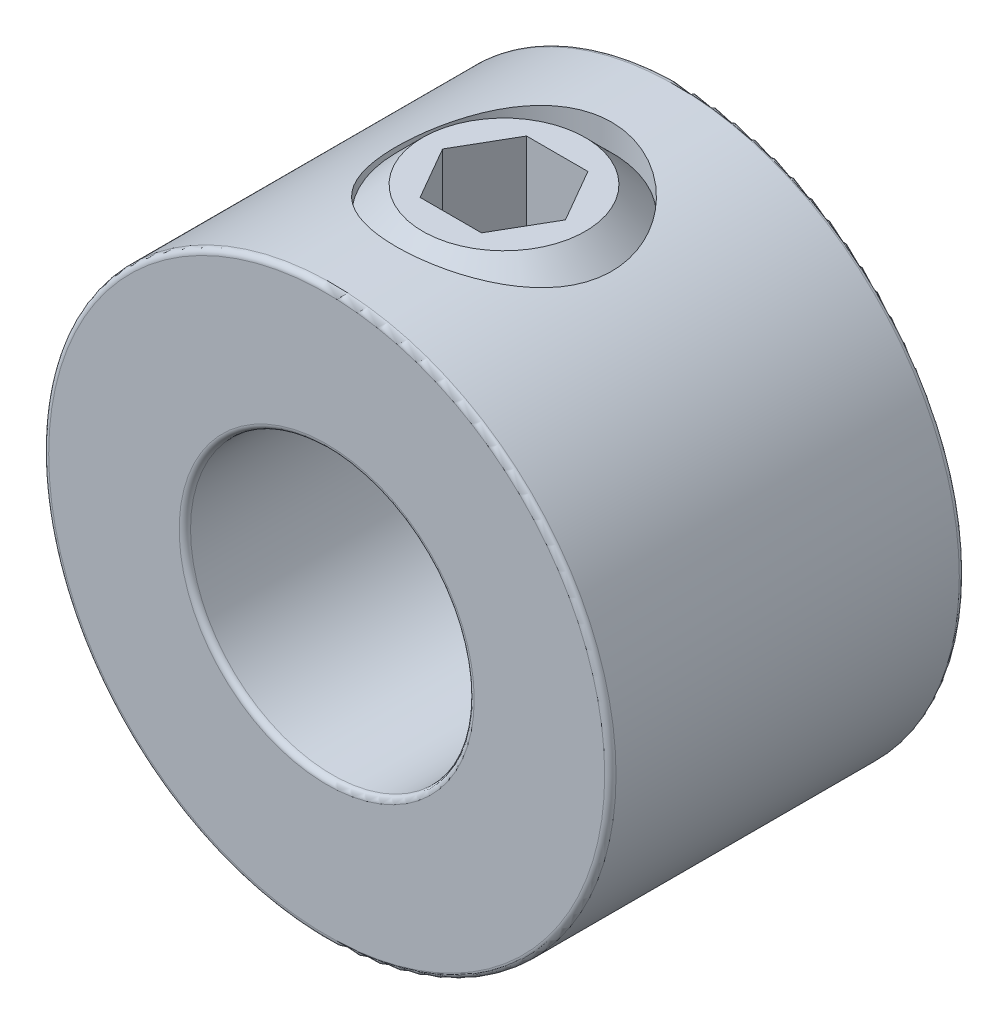
SolidWorks part; units mm, degrees
material "Alliage 1060"
ref_plane "Front Plane" through (0, 0, 0) normal (0, 0, 1) x (1, 0, 0)
ref_plane "Top Plane" through (0, 0, 0) normal (0, 1, 0) x (1, 0, 0)
ref_plane "Right Plane" through (0, 0, 0) normal (1, 0, 0) x (0, 0, -1)
sketch "Sketch1" plane through (0, 0, 0) normal (0, 0, 1) x (1, 0, 0)
  circle A0 centre (0, 0) radius 6.35
  circle A1 centre (0, 0) radius 3.175
  point P4 (6.35, 0)
  dimension "Bore Dia" = 6.35
  dimension "OD" = 12.7
extrude "Extrude1" add sketch "Sketch1" along normal mid plane 7.9375
sketch "Sketch2" plane through (41.275, 0, 0) normal (0, -1, 0) x (0, 0, -1)
  line L0 (3.9688, -41.275) -> (-3.9688, -41.275) construction
  line L1 (-3.9688, -34.925) -> (-3.9688, -47.625) construction
  line L2 (3.9688, -47.625) -> (3.9688, -34.925) construction
  circle A0 centre (0, -41.275) radius 2.413
  point P7 (0, -43.688)
  dimension "Set Screw Dia" = 4.826
extrude "Cut-Extrude1" cut sketch "Sketch2" against normal through all
fillet "Fillet1" radius 0.127 4 edges at (3.175, 0, -3.9688) (3.175, 0, 3.9688) (6.35, 0, -3.9688) (6.35, 0, 3.9688)
sketch "Sketch3" plane through (0, 0, 0) normal (0, 0, 1) x (1, 0, 0)
  line L0 (-1.8198, 3.175) -> (-0.7119, 3.175)
  line L1 (0, 3.8869) -> (-0.7119, 3.175)
  line L2 (0, 3.8869) -> (0, 6.35)
  line L3 (0, 6.35) -> (-1.8198, 6.35)
  line L4 (-2.413, 3.7682) -> (-2.413, 5.7568)
  line L5 (0, 3.175) -> (0, 0) construction
  line L6 (-2.413, 3.7682) -> (-2.413, 3.175) construction
  line L7 (-2.413, 3.175) -> (-1.8198, 3.175) construction
  line L8 (-2.413, 5.7568) -> (-2.413, 6.35) construction
  line L9 (-1.8198, 3.175) -> (-2.413, 3.7682)
  line L10 (-2.413, 5.7568) -> (-1.8198, 6.35)
  line L11 (-2.413, 6.35) -> (-1.8198, 6.35) construction
  line L12 (-0.7119, 3.175) -> (0, 3.175) construction
  line L13 (0, 3.175) -> (0, 3.8869) construction
  circle A1 centre (0, 0) radius 3.175 construction
  dimension "Screw Length" = 3.175
  dimension "D2" = 0.5932
  dimension "D1" = 0.7119
revolve "Revolve1" add sketch "Sketch3" angle 360 about L5
sketch "Sketch4" plane through (3.3734, 6.35, 0) normal (0, -1, 0) x (0, 0, -1)
  line L1 (0, -1.9986) -> (-1.1906, -2.686)
  line L2 (-1.1906, -2.686) -> (-1.1906, -4.0608)
  line L3 (-1.1906, -4.0608) -> (0, -4.7483)
  line L4 (0, -4.7483) -> (1.1906, -4.0608)
  line L5 (1.1906, -4.0608) -> (1.1906, -2.686)
  line L6 (1.1906, -2.686) -> (0, -1.9986)
  circle A0 centre (0, -3.3734) radius 1.1906 construction
  circle A1 centre (0, -3.3734) radius 1.3748 construction
  dimension "D1" = 2.7496
  dimension "Hex Size" = 2.3813
extrude "Cut-Extrude2" cut sketch "Sketch4" along normal blind 2.3813
equation "\"D1@Fillet1\" = \"OD@Sketch1\"*.01"
equation "\"D1@Cut-Extrude2\" = \"Hex Size@Sketch4\""
equation "\"D2@Sketch3\" =(\"Set Screw Dia@Sketch2\"-\"D1@Sketch4\")/3.5"
equation "\"D1@Sketch3\" = \"D2@Sketch3\"*1.2"
